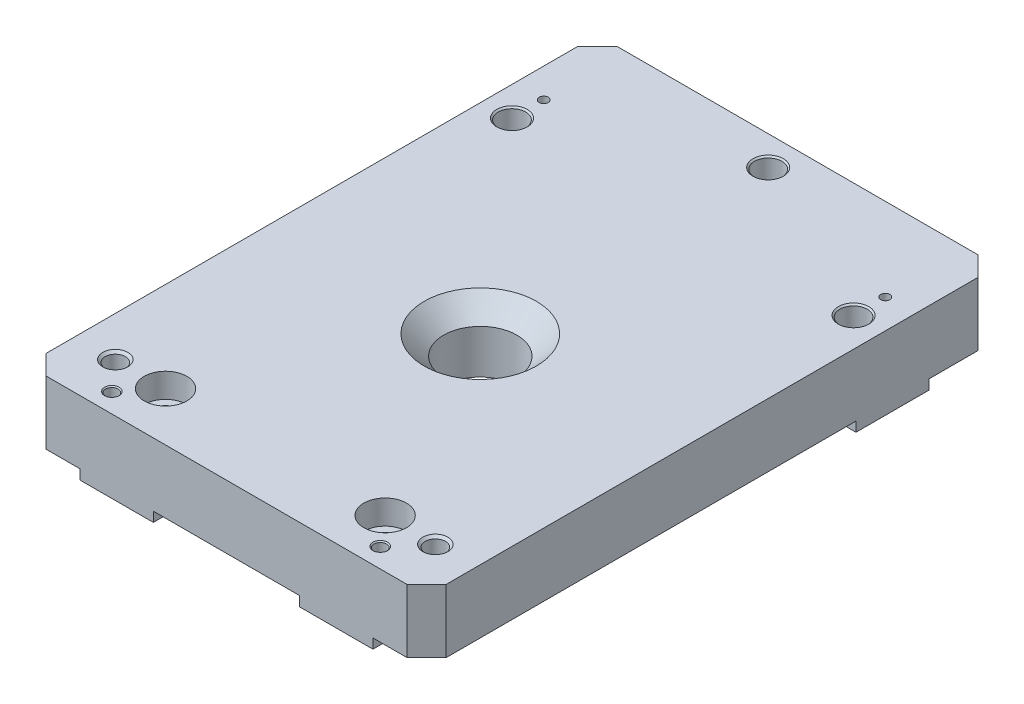
SolidWorks part; units mm, degrees
material "6061-T6 Al"
ref_plane "Front" through (0, 0, 0) normal (0, 0, 1) x (1, 0, 0)
ref_plane "Top" through (0, 0, 0) normal (0, 1, 0) x (1, 0, 0)
ref_plane "Right" through (0, 0, 0) normal (1, 0, 0) x (0, 0, -1)
sketch "Sketch41" plane through (0, 0, 0) normal (0, 1, 0) x (1, 0, 0)
  line L4 (52.07, -110.49) -> (-52.07, -110.49)
  line L5 (52.07, -110.49) -> (52.07, 38.1)
  line L6 (-52.07, -110.49) -> (-52.07, 38.1)
  line L7 (-52.07, 38.1) -> (52.07, 38.1)
  circle A1 centre (0, -44.45) radius 9.525
  dimension "D1" = 52.07
  dimension "D2" = 52.07
  dimension "D3" = 38.1
  dimension "D4" = 110.49
  dimension "D5" = 44.45
extrude "Extrude16" add sketch "Sketch41" along normal blind 16.51 separate body
sketch "Sketch42" plane through (0, 0, 0) normal (0, -1, 0) x (1, 0, 0)
  line L15 (-19.05, 91.44) -> (-19.05, 110.49)
  line L16 (38.1, -20.32) -> (52.07, -20.32)
  line L17 (38.1, -1.27) -> (38.1, -20.32)
  line L18 (52.07, -1.27) -> (38.1, -1.27)
  line L19 (6.35, -38.1) -> (6.35, -22.86)
  line L20 (6.35, -22.86) -> (-6.35, -22.86)
  line L21 (-6.35, -22.86) -> (-6.35, -38.1)
  line L22 (-52.07, -20.32) -> (-38.1, -20.32)
  line L23 (-38.1, -20.32) -> (-38.1, -1.27)
  line L24 (-38.1, -1.27) -> (-52.07, -1.27)
  line L25 (19.05, 110.49) -> (19.05, 91.44)
  line L26 (38.1, 91.44) -> (38.1, 110.49)
  line L27 (19.05, 91.44) -> (38.1, 91.44)
  line L28 (-38.1, 91.44) -> (-19.05, 91.44)
  line L29 (-38.1, 110.49) -> (-38.1, 91.44)
  line L30 (-38.1, 110.49) -> (-19.05, 110.49)
  line L31 (19.05, 110.49) -> (38.1, 110.49)
  line L32 (-6.35, -38.1) -> (6.35, -38.1)
  line L33 (52.07, -20.32) -> (52.07, -1.27)
  line L34 (-52.07, -20.32) -> (-52.07, -1.27)
  dimension "D1" = 19.05
  dimension "D2" = 19.05
  dimension "D3" = 38.1
  dimension "D4" = 38.1
  dimension "D5" = 91.44
  dimension "D6" = 110.49
  dimension "D7" = 38.1
  dimension "D8" = 38.1
  dimension "D9" = 52.07
  dimension "D10" = 52.07
  dimension "D11" = 1.27
  dimension "D12" = 20.32
  dimension "D13" = 22.86
  dimension "D14" = 38.1
  dimension "D15" = 6.35
  dimension "D16" = 6.35
extrude "Extrude17" add sketch "Sketch42" along normal blind 2.54
hole_wizard "1/4 Clearance Hole3" positions "Sketch44" profile "Sketch43" hole size "1/4" standard "Ansi Inch" end condition through all
sketch "Sketch44" plane through (0, -2.54, 0) normal (0, -1, 0) x (1, 0, 0)
  point P0 (-44.45, -8.255)
  point P3 (44.45, -8.255)
  point P10 (0, -30.48)
  dimension "D1" = 44.45
  dimension "D2" = 8.255
  dimension "D3" = 44.45
  dimension "D4" = 30.48
sketch "Sketch43" plane through (-44.45, -2.54, -8.255) normal (1, 0, 0) x (0, 0, -1)
  line L0 (0, 0) -> (0, 19.05)
  line L1 (0, 19.05) -> (3.9624, 19.05)
  line L2 (3.5712, 18.6588) -> (3.5712, 0.3912)
  line L3 (3.5712, 0.3912) -> (3.9624, 0)
  line L5 (3.9624, 0) -> (0, 0)
  line L6 (-3.5712, 0.3912) -> (-3.9624, 0) construction
  line L7 (3.9624, 19.05) -> (3.5712, 18.6588)
  line L8 (-3.9624, 19.05) -> (-3.5712, 18.6588) construction
  line L11 (0, -6.35) -> (0, 107.95) construction
  dimension "Thru Hole Dia." = 7.1425
  dimension "Thru Hole Depth" = 19.05
  dimension "Near C'Sink Dia." = 7.9248
  dimension "Near C'Sink Angle" = 90
  dimension "Far C'Sink Dia." = 7.9248
  dimension "Far C'Sink Angle" = 90
hole_wizard "Press Pin holes for Magnet Bracket Pins" positions "Sketch40" profile "Sketch39" counterbore size "3/8" standard "Ansi Inch"
sketch "Sketch40" plane through (-44.4558, -2.54, 1.2483) normal (0, -1, 0) x (1, 0, 0)
  point P0 (0.0058, -17.7583)
  point P3 (88.9058, -17.7583)
  dimension "D1" = 16.51
  dimension "D2" = 44.45
  dimension "D3" = 44.45
sketch "Sketch39" plane through (-44.45, -2.54, -16.51) normal (1, 0, 0) x (0, 0, -1)
  line L0 (0, 0) -> (0, 7.3039)
  line L1 (0, 7.3039) -> (1.5875, 6.35)
  line L2 (1.5875, 6.35) -> (1.5875, 1.524)
  line L3 (1.5875, 1.524) -> (1.6002, 1.524)
  line L5 (1.6002, 1.524) -> (1.6002, 0.3048)
  line L6 (1.6002, 0.3048) -> (1.905, 0)
  line L7 (1.905, 0) -> (0, 0)
  line L8 (-1.6002, 0.3048) -> (-1.905, 0) construction
  line L10 (0, 7.3039) -> (-1.5875, 6.35) construction
  line L11 (0, -6.35) -> (0, 107.95) construction
  dimension "Hole Dia." = 3.175
  dimension "Hole Depth" = 6.35
  dimension "C'Bore Dia." = 3.2004
  dimension "C'Bore Depth" = 1.524
  dimension "Near C'Sink Dia." = 3.81
  dimension "Near C'Sink Angle" = 90
  dimension "Drill Angle" = 118
hole_wizard "3/32 (0.09375) Diameter Hole1" positions "Sketch48" profile "Sketch47" hole size "3/32" standard "Ansi Inch" end condition through all
sketch "Sketch48" plane through (0, 16.51, 0) normal (0, 1, 0) x (-1, 0, 0)
  point P0 (44.45, -16.51)
  point P3 (-44.45, -16.51)
sketch "Sketch47" plane through (-44.45, 16.51, -16.51) normal (1, 0, 0) x (0, 0, 1)
  line L0 (0, 0) -> (0, 19.05)
  line L1 (0, 19.05) -> (1.1906, 19.05)
  line L2 (1.1906, 19.05) -> (1.1906, 0)
  line L5 (1.1906, 0) -> (0, 0)
  line L11 (0, -6.35) -> (0, 107.95) construction
  dimension "Thru Hole Dia." = 2.3812
  dimension "Thru Hole Depth" = 19.05
hole_wizard "CBORE for 1/4 Socket Head Cap Screw1" positions "Sketch8" profile "Sketch7" counterbore size "1/4" standard "Ansi Inch" end condition through all
sketch "Sketch8" plane through (-41.8365, 16.51, -4.1372) normal (0, 1, 0) x (-1, 0, 0)
  point P0 (-13.2615, 101.9272)
  point P1 (-70.4115, 101.9272)
  dimension "D1" = 28.575
  dimension "D2" = 97.79
  dimension "D3" = 28.575
sketch "Sketch7" plane through (-28.575, 16.51, 97.79) normal (1, 0, 0) x (0, 0, 1)
  line L0 (0, 0) -> (0, 19.05)
  line L1 (3.5712, 18.6589) -> (3.9624, 19.05)
  line L2 (3.5712, 18.6589) -> (3.5712, 6.35)
  line L3 (3.5712, 6.35) -> (5.5562, 6.35)
  line L4 (5.5562, 6.35) -> (5.5562, 0)
  line L5 (5.5562, 0) -> (0, 0)
  line L11 (0, -6.35) -> (0, 107.95) construction
  line L12 (3.9624, 19.05) -> (0, 19.05)
  line L13 (-3.5712, 18.6589) -> (-3.9624, 19.05) construction
  dimension "Thru Hole Dia." = 7.1425
  dimension "Thru Hole Depth" = 19.05
  dimension "C'Bore Dia." = 11.1125
  dimension "C'Bore Depth" = 6.35
  dimension "Far C'Sink Dia." = 7.9248
  dimension "Far C'Sink Angle" = 90
hole_wizard "1/8 (0.125) Diameter Hole1" positions "Sketch46" profile "Sketch45" hole size "1/8" standard "Ansi Inch" end condition through all
sketch "Sketch46" plane through (0, -2.54, 0) normal (0, -1, 0) x (1, 0, 0)
  line L1 (-34.925, 105.41) -> (34.925, 105.41) construction
  circle A2 centre (-28.575, 97.79) radius 3.9624 construction
  circle A3 centre (28.575, 97.79) radius 3.5712 construction
  point P0 (-34.925, 105.41)
  point P3 (34.925, 105.41)
  dimension "D1" = 7.62
  dimension "D3" = 6.35
  dimension "D2" = 6.35
sketch "Sketch45" plane through (-34.925, -2.54, 105.41) normal (1, 0, 0) x (0, 0, -1)
  line L0 (0, 0) -> (0, 19.05)
  line L1 (0, 19.05) -> (1.905, 19.05)
  line L2 (1.6319, 18.7769) -> (1.6319, 0.2731)
  line L3 (1.6319, 0.2731) -> (1.905, 0)
  line L5 (1.905, 0) -> (0, 0)
  line L6 (-1.6319, 0.2731) -> (-1.905, 0) construction
  line L7 (1.905, 19.05) -> (1.6319, 18.7769)
  line L8 (-1.905, 19.05) -> (-1.632, 18.7769) construction
  line L11 (0, -6.35) -> (0, 107.95) construction
  dimension "Thru Hole Dia." = 3.2639
  dimension "Thru Hole Depth" = 19.05
  dimension "Near C'Sink Dia." = 3.81
  dimension "Near C'Sink Angle" = 90
  dimension "Far C'Sink Dia." = 3.81
  dimension "Far C'Sink Angle" = 90
hole_wizard "Tapped Hole for #8-32 Helicoil1" positions "Sketch38" profile "Sketch37" tap size "#8-32" standard "Helicoil® Inch" end condition through all
sketch "Sketch38" plane through (-24.6554, 16.51, -20.5843) normal (0, 1, 0) x (-1, 0, 0)
  line L0 (3.9196, 118.3743) -> (16.9898, 118.3743) construction
  line L2 (3.9196, 118.3743) -> (-66.3006, 118.3743) construction
  circle A0 centre (10.2696, 125.9943) radius 1.6319 construction
  circle A1 centre (-59.5804, 125.9943) radius 1.6319 construction
  point P0 (16.9898, 118.3743)
  point P5 (-66.3006, 118.3743)
  dimension "D1" = 10.16
  dimension "D2" = 10.16
sketch "Sketch37" plane through (-41.6452, 16.51, 97.79) normal (1, 0, 0) x (0, 0, 1)
  line L0 (0, 0) -> (0, 19.05)
  line L1 (0, 19.05) -> (2.1971, 19.05)
  line L3 (2.1971, 19.05) -> (2.1971, 13.0048)
  line L4 (2.6378, 13.0048) -> (2.1971, 13.0048)
  line L5 (2.6378, 13.0048) -> (2.6378, 0.635)
  line L6 (2.6378, 0.635) -> (3.2728, 0)
  line L7 (3.2728, 0) -> (0, 0)
  line L8 (-2.6378, 0.635) -> (-3.2728, 0) construction
  line L11 (0, -6.35) -> (0, 107.95) construction
  dimension "Thru Tap Drill Dia." = 4.3942
  dimension "Thru Tap Drill Depth" = 19.05
  dimension "Thread Major Dia." = 5.2756
  dimension "Thread Depth" = 13.0048
  dimension "Near C'Sink Dia." = 6.5456
  dimension "Near C'Sink Angle" = 90
chamfer "Chamfer1" distance 5.08 angle 45 5 edges at (52.07, 8.255, 110.49) (-52.07, 8.255, 110.49) (-52.07, 8.255, -38.1) (52.07, 8.255, -38.1) (0, 16.51, 53.975)
